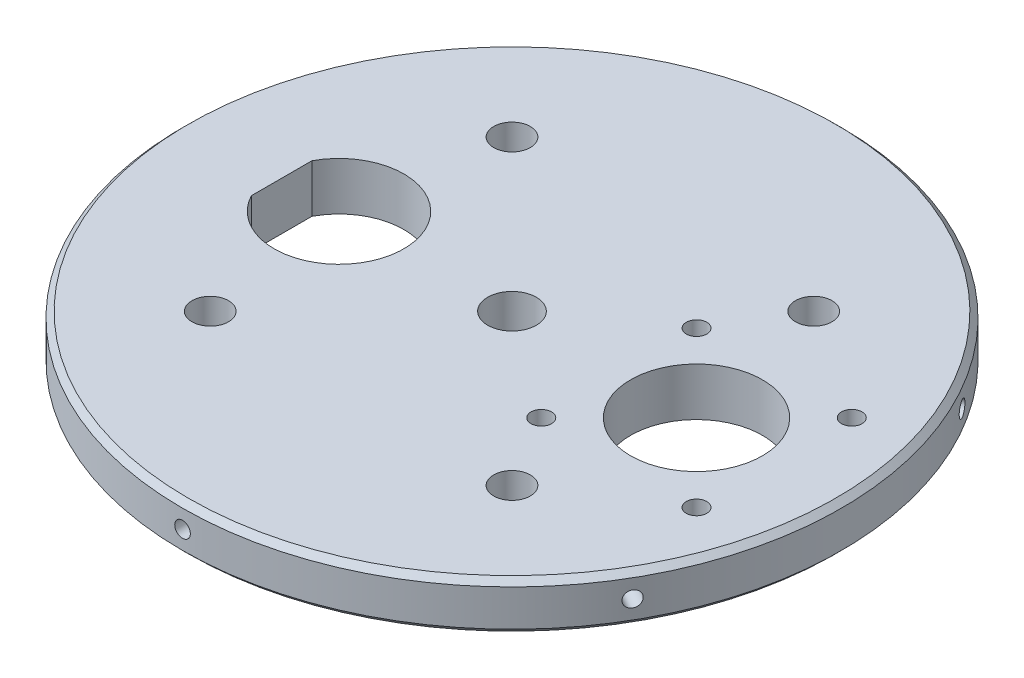
SolidWorks part; units mm, degrees
ref_plane "Front Plane" through (0, 0, 0) normal (0, 0, 1) x (1, 0, 0)
ref_plane "Top Plane" through (0, 0, 0) normal (0, 1, 0) x (1, 0, 0)
ref_plane "Right Plane" through (0, 0, 0) normal (1, 0, 0) x (0, 0, -1)
sketch "Sketch2" plane through (0, 0, 0) normal (0, 1, 0) x (1, 0, 0)
  circle A0 centre (0, 0) radius 57.15
  dimension "D1" = 114.3
extrude "Boss-Extrude1" add sketch "Sketch2" along normal blind 8.35 contours A0
sketch "Sketch6" plane through (0, 8.35, 0) normal (0, 1, 0) x (1, 0, 0)
  circle A0 centre (-26.1629, -26.1629) radius 3.175
  circle A1 centre (26.1629, -26.1629) radius 3.175
  circle A2 centre (-26.1629, 26.1631) radius 3.175
  circle A3 centre (26.1629, 26.1631) radius 3.175
  dimension "D1" = 6.35
  dimension "D2" = 74
  dimension "D3" = 26.1629
  dimension "D4" = 26.1629
  dimension "D5" = 26.1629
extrude "Cut-Extrude1" cut sketch "Sketch6" against normal up to next
sketch "Sketch7" plane through (0, 8.35, 0) normal (0, 1, 0) x (1, 0, 0)
  circle A0 centre (32, 0) radius 11.43
  circle A3 centre (18.54, -13.464) radius 1.778
  circle A4 centre (18.54, 13.46) radius 1.778
  circle A5 centre (45.46, 13.46) radius 1.778
  circle A6 centre (45.46, -13.464) radius 1.778
  dimension "D1" = 22.86
  dimension "D2" = 3.556
  dimension "D3" = 3.556
  dimension "D4" = 3.556
  dimension "D5" = 3.556
  dimension "D6" = 13.46
  dimension "D7" = 13.46
  dimension "D8" = 13.46
  dimension "D9" = 13.464
  dimension "D10" = 32
extrude "Cut-Extrude2" cut sketch "Sketch7" against normal through all
sketch "Sketch8" plane through (0, 8.35, 0) normal (0, 1, 0) x (1, 0, 0)
  line L0 (-39.95, 5.2498) -> (-39.95, -5.2498)
  circle A2 centre (0, 0) radius 4.2164
  arc A3 (-39.95, -5.2498) -> (-39.95, 5.2498) centre (-30, 0) ccw
  dimension "D1" = 9.95
  dimension "D3" = 8.4328
  dimension "D4" = 22.5
  dimension "D5" = 30
extrude "Cut-Extrude3" cut sketch "Sketch8" against normal through all
chamfer "Chamfer1" distance 1 angle 45 2 edges at (0, 0, 57.15) (0, 8.35, 57.15)
ref_plane "Plane1" through (0, 0, 57.15) normal (0, 0, 1) x (1, 0, 0)
sketch "Sketch9" plane through (0, 0, 57.15) normal (0, 0, 1) x (1, 0, 0)
  line L0 (56.15, 8.35) -> (-56.15, 8.35) construction
  point P0 (0, 4.175)
  dimension "D1" = 4.175
hole_wizard "#6-32 Tapped Hole1" positions "3DSketch2" profile "Sketch11" tap size "#6-32" standard "ANSI Inch"
sketch3d "3DSketch2"
  point P0 (0, 4.175, 57.15)
  point P4 (0, 4.175, 57.15)
sketch "Sketch11" plane through (0, 4.175, 57.15) normal (1, 0, 0) x (0, -1, 0)
  line L0 (0, 0) -> (0, 13.8127)
  line L1 (0, 13.8127) -> (1.3525, 13)
  line L2 (1.3525, 13) -> (1.3525, 0)
  line L5 (1.3525, 0) -> (0, 0)
  line L10 (0, 13.8127) -> (-1.3526, 13) construction
  line L11 (0, -6.35) -> (0, 107.95) construction
  dimension "Tap Drill Dia." = 2.7051
  dimension "Tap Drill Depth" = 13
  dimension "Drill Angle" = 118
cosmetic thread "Hole Thread2" parameters "D1"=12.7, "D2"=3.5052
pattern_circular "CirPattern1" count 6 over 360 about axis through (0, 1, 0) along (0, 1, 0) of "#6-32 Tapped Hole1"
cosmetic thread "Hole Thread3" parameters "D1"=12.7, "D2"=3.5052
cosmetic thread "Hole Thread5" parameters "D1"=12.7, "D2"=3.5052
cosmetic thread "Hole Thread8" parameters "D1"=12.7, "D2"=3.5052
cosmetic thread "Hole Thread9" parameters "D1"=12.7, "D2"=3.5052
cosmetic thread "Hole Thread10" parameters "D1"=12.7, "D2"=3.5052
equation "\"width\"=26.1629"
equation "\"D4@Sketch6\"=\"width\""
equation "\"D3@Sketch6\"=\"width\""
equation "\"D5@Sketch6\"=\"width\""
